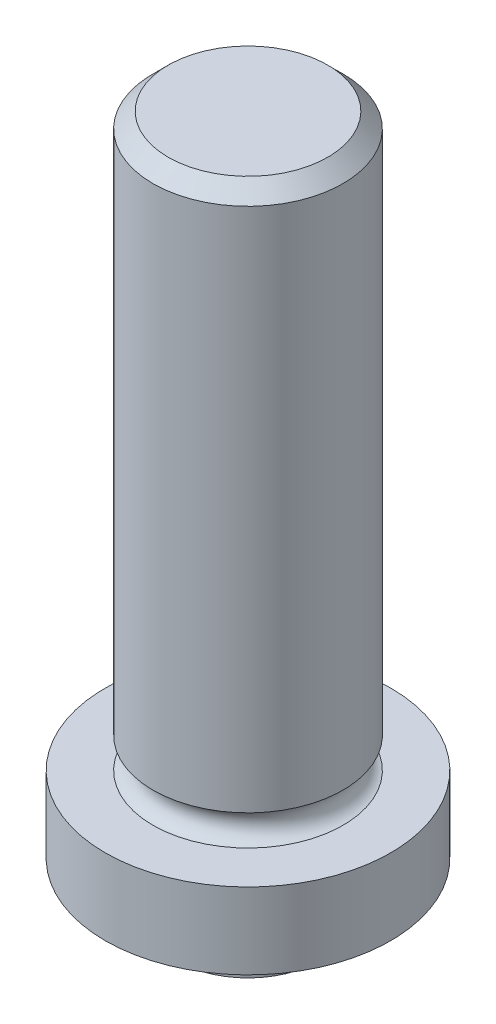
SolidWorks part; units mm, degrees
ref_plane "Front Plane" through (0, 0, 0) normal (0, 0, 1) x (1, 0, 0)
ref_plane "Top Plane" through (0, 0, 0) normal (0, 1, 0) x (1, 0, 0)
ref_plane "Right Plane" through (0, 0, 0) normal (1, 0, 0) x (0, 0, -1)
sketch "Sketch1" plane through (0, 0, 0) normal (0, 0, 1) x (1, 0, 0)
  line L0 (0, 0) -> (0, 95.051) construction
  line L1 (0, 23.368) -> (3.1712, 23.368)
  line L2 (3.1712, 23.368) -> (3.1712, 5.334)
  line L3 (3.1712, 4.318) -> (4.7625, 4.318)
  line L4 (4.7625, 4.318) -> (4.7625, 1.778)
  line L5 (4.7625, 1.778) -> (2.3749, 1.778)
  line L6 (2.3749, 1.778) -> (2.3749, 0)
  line L7 (2.3749, 0) -> (0, 0)
  line L8 (0, 0) -> (0, 23.368)
  arc A0 (3.1712, 5.334) -> (3.1712, 4.318) centre (3.2982, 4.826) ccw
  dimension "D8" = 0.127
  dimension "D1" = 19.05
  dimension "D2" = 23.368
  dimension "D3" = 1.778
  dimension "D4" = 6.3424
  dimension "D5" = 9.525
  dimension "D6" = 4.7498
  dimension "D7" = 1.016
revolve "Revolve1" add sketch "Sketch1" angle 360 about L0
fillet "Fillet1" radius 0.127 1 edges at (0, 1.778, -2.3749)
chamfer "Chamfer1" distance 0.508 angle 45 1 edges at (0, 23.368, -3.1712)
